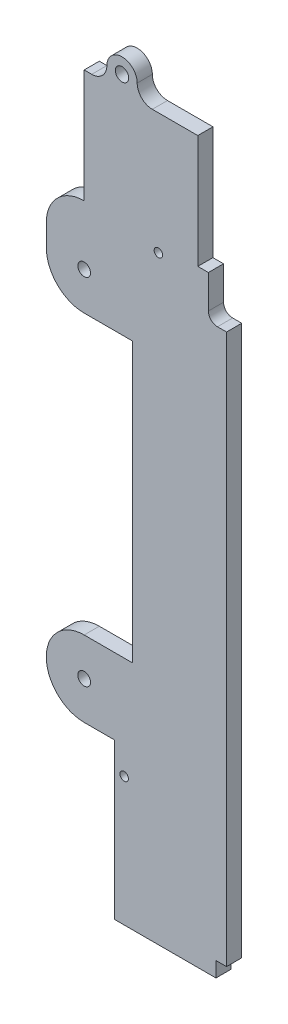
SolidWorks part; units mm, degrees
material "6061-T6 Black anodised"
ref_plane "Front Plane" through (0, 0, 0) normal (0, 0, 1) x (1, 0, 0)
ref_plane "Top Plane" through (0, 0, 0) normal (0, 1, 0) x (1, 0, 0)
ref_plane "Right Plane" through (0, 0, 0) normal (1, 0, 0) x (0, 0, -1)
sketch "Sketch1" plane through (0, 0, 0) normal (0, 0, 1) x (1, 0, 0)
  line L0 (41, 136.6) -> (41, 125.6)
  line L1 (0, 174) -> (2.5, 174)
  line L2 (-12.5, 124.1) -> (-12.5, 117)
  line L3 (10, -29.8) -> (47, -29.8) construction
  line L4 (47, 122.6) -> (47, -29.8)
  line L5 (44, 122.6) -> (47, 122.6)
  line L6 (41, 136.6) -> (37.5, 136.6)
  line L7 (37.5, 136.6) -> (37.5, 174)
  line L8 (0, -12.5) -> (10, -12.5)
  line L9 (10, -12.5) -> (10, -29.8)
  line L10 (0, 12.5) -> (16, 12.5)
  line L11 (16, 12.5) -> (16, 104.5)
  line L12 (16, 104.5) -> (0, 104.5)
  line L13 (47, -29.8) -> (47, -58.8)
  line L14 (22.5, 174) -> (37.5, 174)
  line L15 (0, 136.6) -> (0, 174)
  line L16 (43.5, -63.8) -> (10, -63.8)
  line L17 (10, -63.8) -> (10, -29.8)
  line L18 (43.5, -58.8) -> (47, -58.8)
  line L19 (43.5, -58.8) -> (43.5, -63.8)
  circle A0 centre (0, 0) radius 2.1
  circle A1 centre (0, 117) radius 2.1
  arc A2 (41, 125.6) -> (44, 122.6) centre (44, 125.6) ccw
  arc A3 (0, 12.5) -> (0, -12.5) centre (0, 0) ccw
  arc A4 (-12.5, 117) -> (0, 104.5) centre (0, 117) ccw
  arc A5 (0, 136.6) -> (-12.5, 124.1) centre (0, 124.1) ccw
  circle A6 centre (12.5, 179) radius 2.2
  arc A7 (17.5, 179) -> (7.5, 179) centre (12.5, 179) ccw
  arc A8 (2.5, 174) -> (7.5, 179) centre (2.5, 179) ccw
  arc A9 (17.5, 179) -> (22.5, 174) centre (22.5, 179) ccw
  dimension "D6" = 3
  dimension "D15" = 4.4
  dimension "D19" = 4.2
  dimension "D1" = 12.5
  dimension "D2" = 117
  dimension "D3" = 29.8
  dimension "D4" = 203.8
  dimension "D5" = 47
  dimension "D7" = 6
  dimension "D8" = 51.4
  dimension "D9" = 14
  dimension "D10" = 3.5
  dimension "D11" = 22.5
  dimension "D12" = 28.5
  dimension "D13" = 34
  dimension "D14" = 25
  dimension "D16" = 5
  dimension "D17" = 5
  dimension "D18" = 3.5
extrude "Boss-Extrude1" add sketch "Sketch1" along normal blind 5
sketch "Sketch2" plane through (0, 0, 5) normal (0, 0, 1) x (1, 0, 0)
  circle A0 centre (13.2, -21.3) radius 1.4
  circle A1 centre (24.5, 134) radius 1.4
  circle A2 centre (0, 117) radius 2.1 construction
  dimension "D2" = 13.2
  dimension "D3" = 2.8
  dimension "D5" = 17
  dimension "D1" = 21.3
  dimension "D4" = 24.5
extrude "Cut-Extrude1" cut sketch "Sketch2" against normal through all
